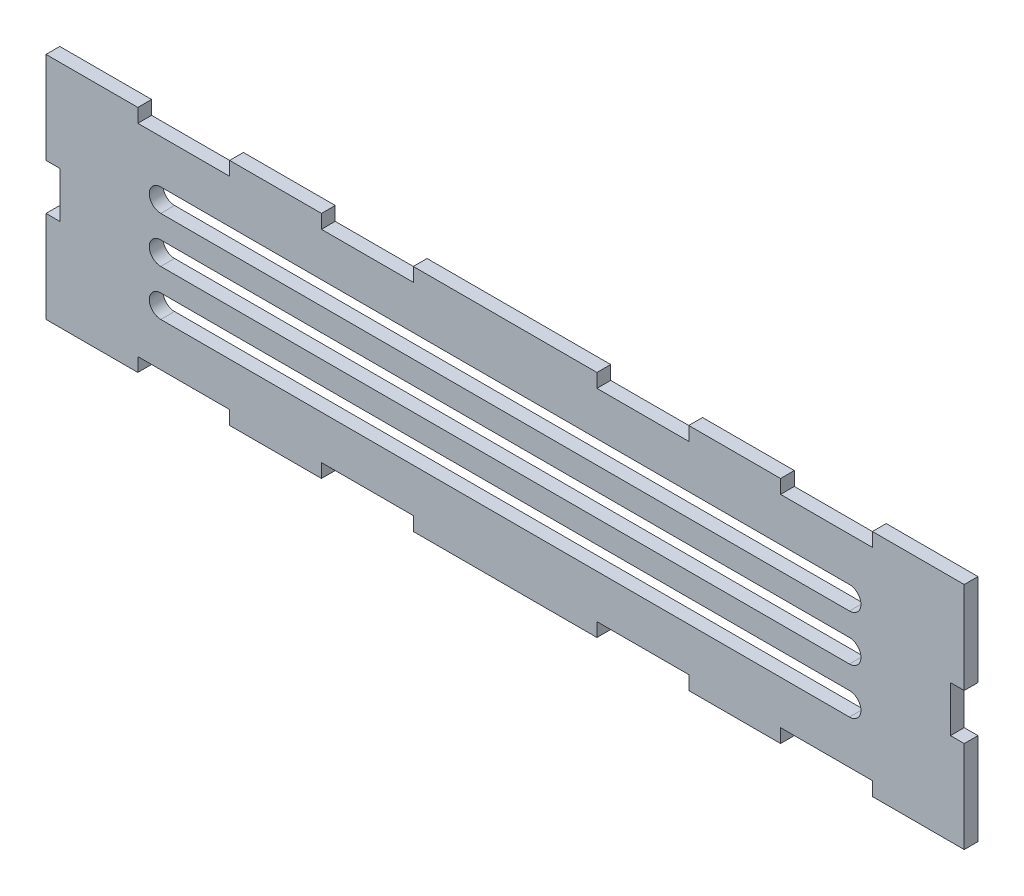
SolidWorks part; units mm, degrees
ref_plane "Front Plane" through (0, 0, 0) normal (0, 0, 1) x (1, 0, 0)
ref_plane "Top Plane" through (0, 0, 0) normal (0, 1, 0) x (1, 0, 0)
ref_plane "Right Plane" through (0, 0, 0) normal (1, 0, 0) x (0, 0, -1)
sketch "Sketch1" plane through (0, 0, 0) normal (0, 0, 1) x (1, 0, 0)
  line L1 (100, -25) -> (-100, -25)
  line L2 (100, -25) -> (100, 25)
  line L3 (100, 25) -> (-100, 25)
  line L4 (-100, -25) -> (-100, 25)
  line L5 (100, -25) -> (-100, 25) construction
  line L6 (100, 25) -> (-100, -25) construction
  point P0 (0, 0)
extrude "Boss-Extrude1" add sketch "Sketch1" along normal blind 3
sketch "Sketch2" plane through (0, 0, 3) normal (0, 0, 1) x (1, 0, 0)
  line L0 (-60, 25) -> (-80, 25)
  line L1 (-60, 22) -> (-80, 22)
  line L2 (-40, -22) -> (-20, -22)
  line L3 (-40, -25) -> (-20, -25)
  line L4 (-100, 25) -> (-100, -25)
  line L5 (-100, -25) -> (100, -25)
  line L6 (100, -25) -> (100, 25)
  line L7 (100, 25) -> (-100, 25)
  line L8 (97, -5) -> (97, 5)
  line L9 (-80, -25) -> (-60, -25)
  line L10 (40, 25) -> (20, 25)
  line L11 (80, 25) -> (60, 25)
  line L12 (-80, 25) -> (-80, 22)
  line L13 (-60, 25) -> (-60, 22)
  line L14 (-40, 25) -> (-40, 22)
  line L15 (-20, 25) -> (-20, 22)
  line L16 (-97, 22) -> (-97, -22)
  line L17 (-97, -22) -> (97, -22)
  line L18 (97, -22) -> (97, 22)
  line L19 (97, 22) -> (-97, 22)
  line L20 (100, -5) -> (100, 5)
  line L21 (-80, -22) -> (-60, -22)
  line L22 (40, 22) -> (20, 22)
  line L23 (80, 22) -> (60, 22)
  line L25 (20, 25) -> (20, 22)
  line L26 (40, 25) -> (40, 22)
  line L27 (60, 25) -> (60, 22)
  line L28 (80, 25) -> (80, 22)
  line L29 (-80, -22) -> (-80, -25)
  line L30 (-60, -22) -> (-60, -25)
  line L31 (-40, -22) -> (-40, -25)
  line L32 (-20, -22) -> (-20, -25)
  line L34 (20, -22) -> (20, -25)
  line L35 (40, -22) -> (40, -25)
  line L36 (60, -22) -> (60, -25)
  line L37 (80, -22) -> (80, -25)
  line L38 (60, -22) -> (80, -22)
  line L39 (100, 5) -> (97, 5)
  line L40 (100, -5) -> (97, -5)
  line L41 (60, -25) -> (80, -25)
  line L42 (-20, 25) -> (-40, 25)
  line L43 (-97, 5) -> (-100, 5)
  line L44 (-97, -5) -> (-100, -5)
  line L45 (-20, 22) -> (-40, 22)
  line L46 (-100, 5) -> (-100, -5)
  line L47 (-97, 5) -> (-97, -5)
  line L48 (100, 15) -> (97, 15) [skipped]
  line L49 (100, -15) -> (97, -15) [skipped]
  line L50 (20, -22) -> (40, -22)
  line L51 (20, -25) -> (40, -25)
  dimension "D1" = 0
  dimension "D2" = 3
  dimension "D3" = 5
extrude "Cut-Extrude1" cut sketch "Sketch2" against normal blind 3
sketch "Sketch3" plane through (0, 0, 3) normal (0, 0, 1) x (1, 0, 0)
  line L5 (75, 10) -> (-75, 10) construction
  line L6 (75, 7.5) -> (-75, 7.5)
  line L7 (75, 12.5) -> (-75, 12.5)
  line L8 (75, 0) -> (-75, 0) construction
  line L9 (75, -2.5) -> (-75, -2.5)
  line L10 (75, 2.5) -> (-75, 2.5)
  line L11 (75, -10) -> (-75, -10) construction
  line L12 (75, -12.5) -> (-75, -12.5)
  line L13 (75, -7.5) -> (-75, -7.5)
  arc A0 (75, 7.5) -> (75, 12.5) centre (75, 10) ccw
  arc A1 (-75, 12.5) -> (-75, 7.5) centre (-75, 10) ccw
  arc A2 (75, -2.5) -> (75, 2.5) centre (75, 0) ccw
  arc A3 (-75, 2.5) -> (-75, -2.5) centre (-75, 0) ccw
  arc A4 (75, -12.5) -> (75, -7.5) centre (75, -10) ccw
  arc A5 (-75, -7.5) -> (-75, -12.5) centre (-75, -10) ccw
  point P12 (0, 10)
  point P18 (0, 0)
  point P25 (0, -10)
extrude "Cut-Extrude2" cut sketch "Sketch3" against normal blind 3
